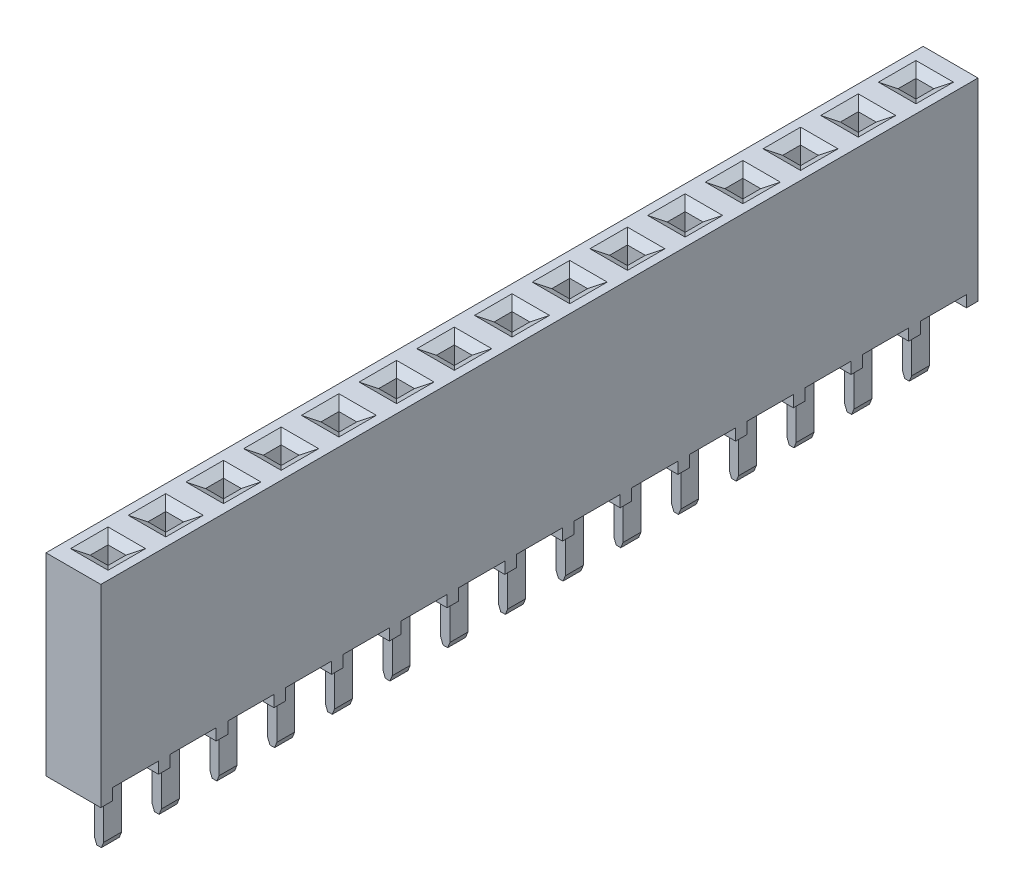
SolidWorks part; units mm, degrees
material "普通碳钢"
ref_plane "Front" through (0, 0, 0) normal (0, 0, 1) x (1, 0, 0)
ref_plane "Top" through (0, 0, 0) normal (0, 1, 0) x (1, 0, 0)
ref_plane "Right" through (0, 0, 0) normal (1, 0, 0) x (0, 0, -1)
sketch "Sketch1" plane through (0, 0, 0) normal (0, 1, 0) x (1, 0, 0)
  line L0 (-1.2065, -19.304) -> (1.2065, 19.304) construction
  line L1 (-1.2065, 19.304) -> (1.2065, 19.304)
  line L2 (-1.2065, 19.304) -> (-1.2065, -19.304)
  line L3 (-1.2065, -19.304) -> (1.2065, -19.304)
  line L4 (1.2065, 19.304) -> (1.2065, -19.304)
  dimension "D1" = 38.608
  dimension "D2" = 2.413
extrude "Main Body" add sketch "Sketch1" along normal blind 8.509
ref_plane "Plane1" through (0, 0, -15.24) normal (0, 0, -1) x (-1, 0, 0)
ref_plane "Plane2" through (0, 0, -17.78) normal (0, 0, -1) x (-1, 0, 0)
ref_plane "Plane3" through (0, 0, 0) normal (0, 0, 1) x (1, 0, 0)
ref_plane "Plane4" through (0, 0, -2.54) normal (0, 0, 1) x (1, 0, 0)
sketch "Sketch5" plane through (1.2065, 0, 0) normal (1, 0, 0) x (0, 0, -1)
  line L0 (-19.304, 0) -> (19.304, 0) construction
  line L1 (16.764, 0) -> (18.796, 0)
  line L2 (16.764, 0) -> (16.764, 0.508)
  line L3 (16.764, 0.508) -> (18.796, 0.508)
  line L4 (18.796, 0) -> (18.796, 0.508)
  line L5 (17.78, 0.7418) -> (17.78, -0.7099) construction
  line L6 (19.304, 8.509) -> (19.304, 0) construction
  dimension "D1" = 0.508
  dimension "D2" = 1.524
  dimension "D3" = 0.508
extrude "Cut-Extrude2" cut sketch "Sketch5" against normal up to next (2.413 mm away)
pattern_linear "LPattern1" count 15 spacing 2.54 along (0, 0, 1) of "Cut-Extrude2"
sketch "Sketch2" plane through (0, 8.509, 0) normal (0, 1, 0) x (-1, 0, 0)
  line L0 (0, -0.6833) -> (0, -4.4888) construction
  line L1 (-0.3937, -18.1737) -> (0.3937, -18.1737)
  line L2 (-0.3937, -18.1737) -> (-0.3937, -17.3863)
  line L3 (-0.3937, -17.3863) -> (0.3937, -17.3863)
  line L4 (0.3937, -18.1737) -> (0.3937, -17.3863)
  line L5 (0, 0) -> (-2.54, 0) construction
  line L6 (0.3937, -18.1737) -> (-0.3937, -17.3863) construction
  line L8 (-1.2065, -19.304) -> (1.2065, -19.304) construction
  line L9 (-1.2065, 19.304) -> (-1.2065, -19.304) construction
  point P8 (0, -17.78)
  dimension "D1" = 1.524
  dimension "D2" = 0.7874
  dimension "D3" = 0.7874
  dimension "D4" = 1.2065
extrude "Cut-Extrude1" cut sketch "Sketch2" against normal through all
chamfer "Chamfer1" distance 0.4318 angle 30 4 edges at (0.3937, 8.509, -17.78) (0, 8.509, -18.1737) (-0.3937, 8.509, -17.78) (0, 8.509, -17.3863)
pattern_linear "LPattern2" count 15 spacing 2.54 along (0, 0, 1) of "Chamfer1", "Cut-Extrude1"
sketch "Sketch4" plane through (0, 0, -17.78) normal (0, 0, -1) x (-1, 0, 0)
  line L0 (0, 2.0688) -> (0, -17.6627) construction
  line L1 (0.3937, 0.508) -> (0.3937, 8.2597) construction
  line L2 (-0.3937, 0.508) -> (-0.3937, 8.2597) construction
  line L3 (-0.3937, 1.016) -> (0.3937, 1.016)
  line L5 (-0.2032, 0.889) -> (-0.2032, -2.3876)
  line L6 (-0.1016, -2.6416) -> (0.1016, -2.6416)
  line L7 (0.2032, 0.889) -> (0.2032, -2.3876)
  line L8 (0.1016, -2.6416) -> (0.2032, -2.3876)
  line L9 (-0.2032, -2.3876) -> (-0.1016, -2.6416)
  line L10 (-1.2065, 0) -> (1.2065, 0) construction
  line L11 (0.3937, 1.016) -> (0.3937, 0.889)
  line L12 (0.3937, 0.889) -> (0.2032, 0.889)
  line L13 (-0.2032, 0.889) -> (-0.3937, 0.889)
  line L14 (-0.3937, 0.889) -> (-0.3937, 1.016)
  dimension "D1" = 0.254
  dimension "D2" = 0.2032
  dimension "D3" = 0.4064
  dimension "D4" = 2.6416
  dimension "D5" = 0.7874
  dimension "D6" = 0.889
  dimension "D7" = 1.016
extrude "PIN" add sketch "Sketch4" along normal mid plane 0.7874
pattern_linear "LPattern4" count 15 spacing 2.54 along (0, 0, 1) of "PIN"
sketch "Sketch7" plane through (0, 0, -17.78) normal (0, 0, -1) x (-1, 0, 0)
  line L0 (-0.2032, 1.016) -> (-0.2032, -0.9144)
  line L1 (0.6096, -1.3208) -> (1.4605, -1.3208)
  line L2 (1.4605, -1.3208) -> (1.4605, -1.7272)
  line L3 (1.4605, -1.7272) -> (0.6096, -1.7272)
  line L4 (0.2032, -0.9144) -> (0.2032, 1.016)
  line L5 (-0.2032, 1.016) -> (-0.3937, 1.016)
  line L6 (0, 1.4788) -> (0, -2.2478) construction
  line L10 (1.2065, 8.509) -> (1.2065, 0) construction
  line L11 (-0.3937, 1.016) -> (-0.3937, 1.27)
  line L12 (-0.3937, 1.27) -> (0.3937, 1.27)
  line L13 (0.3937, 1.27) -> (0.3937, 1.016)
  line L14 (0.3937, 1.016) -> (0.2032, 1.016)
  line L16 (1.4605, -1.524) -> (-2.3476, -1.524) construction
  line L17 (-1.2065, 0) -> (1.2065, 0) construction
  line L18 (1.2065, 0.508) -> (-1.2065, 0.508) construction
  arc A0 (-0.2032, -0.9144) -> (0.6096, -1.7272) centre (0.6096, -0.9144) ccw
  arc A1 (0.6096, -1.3208) -> (0.2032, -0.9144) centre (0.6096, -0.9144) cw
  dimension "D9" = 0.8128
  dimension "D10" = 0.4064
  dimension "D1" = 1.2065
  dimension "D2" = 0.4064
  dimension "D3" = 0.4064
  dimension "D4" = 1.524
  dimension "D6" = 0.7874
  dimension "D7" = 0.762
  dimension "D8" = 0.254
  dimension "A" = 0.254
sketch "Sketch8" plane through (0, 0, -15.24) normal (0, 0, -1) x (-1, 0, 0)
  line L0 (0.2032, 1.016) -> (0.2032, -0.9144)
  line L1 (-0.3937, 1.27) -> (0.3937, 1.27)
  line L2 (1.2065, 8.509) -> (1.2065, 0) construction
  line L3 (0.3937, 1.016) -> (0.2032, 1.016)
  line L5 (-0.3937, 1.016) -> (-0.3937, 1.27)
  line L6 (0.3937, 1.016) -> (0.3937, 1.27)
  line L7 (-1.2065, 0) -> (1.2065, 0) construction
  line L8 (-0.2032, 1.016) -> (-0.2032, -0.9144)
  line L9 (0, 1.9479) -> (0, -2.4889) construction
  line L10 (2.9301, -1.524) -> (0.4606, -1.524) construction
  line L11 (1.2065, 8.509) -> (1.2065, 0) construction
  line L13 (-0.2032, 1.016) -> (-0.2032, -3.4544)
  line L15 (0.6096, -1.7272) -> (1.4605, -1.7272)
  line L16 (1.4605, -1.7272) -> (1.4605, -1.3208)
  line L17 (1.4605, -1.3208) -> (0.6096, -1.3208)
  line L18 (0.6096, -4.2672) -> (1.4605, -4.2672)
  line L19 (0.2032, -3.4544) -> (0.2032, 1.016)
  line L20 (1.4605, -3.8608) -> (0.6096, -3.8608)
  line L21 (1.4605, -4.2672) -> (1.4605, -3.8608)
  line L22 (0.3937, 1.27) -> (-0.3937, 1.27)
  line L23 (-0.3937, 1.016) -> (-0.2032, 1.016)
  line L24 (0.2032, 1.016) -> (0.3937, 1.016)
  line L25 (0.3937, 1.016) -> (0.3937, 1.27)
  line L26 (-0.3937, 1.016) -> (-0.3937, 1.27)
  line L27 (0.3937, 0.508) -> (0.3937, 0.889) construction
  line L28 (-0.3937, 0.508) -> (-0.3937, 0.889) construction
  line L29 (0, 1.27) -> (0, -2.4889) construction
  line L30 (1.4605, -4.064) -> (1.27, -4.064) construction
  line L31 (-0.2032, 1.016) -> (-0.3937, 1.016)
  arc A0 (0.6096, -3.8608) -> (0.2032, -3.4544) centre (0.6096, -3.4544) cw
  arc A1 (0.6096, -4.2672) -> (-0.2032, -3.4544) centre (0.6096, -3.4544) cw
  arc A2 (0.6096, -1.7272) -> (-0.2032, -0.9144) centre (0.6096, -0.9144) cw
  arc A3 (0.6096, -1.3208) -> (0.2032, -0.9144) centre (0.6096, -0.9144) cw
  dimension "D5" = 0.8128
  dimension "D6" = 0.4064
  dimension "D14" = 0.4064
  dimension "D15" = 0.8128
  dimension "D1" = 1.27
  dimension "D2" = 0.254
  dimension "D3" = 0.4064
  dimension "D4" = 0.4064
  dimension "D7" = 1.524
  dimension "D8" = 0.4064
  dimension "D9" = 0.254
  dimension "D10" = 2.54
  dimension "D11" = 0.4064
  dimension "D12" = 1.2065
sketch "Sketch9" plane through (0, 0, -15.24) normal (0, 0, -1) x (-1, 0, 0)
  line L0 (0, 1.6049) -> (0, -3.2713) construction
  line L1 (-2.9337, 1.016) -> (-2.9337, 1.27)
  line L2 (0.3937, 1.27) -> (-0.3937, 1.27)
  line L4 (-2.1463, 1.27) -> (-2.9337, 1.27)
  line L5 (0.3937, 1.016) -> (0.3937, 1.27)
  line L6 (-2.3368, 1.016) -> (-2.1463, 1.016)
  line L7 (-0.3937, 1.016) -> (-0.3937, 1.27)
  line L8 (-0.3937, 1.016) -> (-0.2032, 1.016)
  line L10 (0.3937, 1.27) -> (-0.3937, 1.27)
  line L11 (-2.1463, 1.27) -> (-2.1463, 1.016)
  line L12 (-1.9304, -4.2672) -> (1.4605, -4.2672)
  line L13 (1.4605, -4.2672) -> (1.4605, -3.8608)
  line L14 (1.4605, -3.8608) -> (-1.9304, -3.8608)
  line L15 (0.2032, -5.9944) -> (0.2032, 1.016)
  line L16 (-0.3937, 1.016) -> (-0.3937, 1.27)
  line L17 (-0.2032, 1.016) -> (-0.2032, -5.9944)
  line L18 (-0.3937, 1.016) -> (-0.2032, 1.016)
  line L19 (0.2032, 1.016) -> (0.3937, 1.016)
  line L20 (0.3937, 1.27) -> (0.3937, 1.016)
  line L21 (0.2032, -0.9144) -> (0.2032, 1.016)
  line L22 (-0.2032, 1.016) -> (-0.2032, -0.9144)
  line L24 (1.2065, 8.509) -> (1.2065, 0) construction
  line L25 (1.4605, -1.7272) -> (1.4605, -1.3208)
  line L26 (1.4605, -1.3208) -> (0.6096, -1.3208)
  line L27 (-2.3368, -3.4544) -> (-2.3368, 1.016)
  line L29 (-2.7432, 1.016) -> (-2.7432, -3.4544)
  line L31 (-1.2065, 0) -> (1.2065, 0) construction
  line L32 (0.6096, -1.7272) -> (1.4605, -1.7272)
  line L34 (6.2865, -1.524) -> (4.283, -1.524) construction
  line L35 (6.2865, -4.064) -> (4.7316, -4.064) construction
  line L40 (-2.7432, 1.016) -> (-2.9337, 1.016)
  line L41 (-2.54, 1.27) -> (-2.54, -1.7272) construction
  line L42 (0.2032, 1.016) -> (0.3937, 1.016)
  line L43 (0.3937, 0.508) -> (0.3937, 0.889) construction
  line L44 (-0.3937, 0.508) -> (-0.3937, 0.889) construction
  line L45 (0, 1.27) -> (0, -1.198) construction
  line L46 (0.6096, -6.4008) -> (1.4605, -6.4008)
  line L47 (1.4605, -6.4008) -> (1.4605, -6.8072)
  line L48 (1.4605, -6.8072) -> (0.6096, -6.8072)
  line L49 (6.1112, -6.604) -> (4.5563, -6.604) construction
  arc A0 (0.2032, -0.9144) -> (0.6096, -1.3208) centre (0.6096, -0.9144) ccw
  arc A1 (-0.2032, -0.9144) -> (0.6096, -1.7272) centre (0.6096, -0.9144) ccw
  arc A2 (-1.9304, -4.2672) -> (-2.7432, -3.4544) centre (-1.9304, -3.4544) cw
  arc A3 (-1.9304, -3.8608) -> (-2.3368, -3.4544) centre (-1.9304, -3.4544) cw
  arc A4 (0.6096, -6.4008) -> (0.2032, -5.9944) centre (0.6096, -5.9944) cw
  arc A5 (0.6096, -6.8072) -> (-0.2032, -5.9944) centre (0.6096, -5.9944) cw
  dimension "D7" = 1.27
  dimension "D8" = 0.254
  dimension "D11" = 0.4064
  dimension "D12" = 0.8128
  dimension "D4" = 0.4064
  dimension "D5" = 0.8128
  dimension "D15" = 0.4064
  dimension "D16" = 0.8128
  dimension "D2" = 1.524
  dimension "D3" = 0.4064
  dimension "D6" = 0.4064
  dimension "D9" = 1.2065
  dimension "D10" = 2.54
  dimension "D13" = 0.4064
  dimension "D14" = 5.08
  dimension "D17" = 0.4064
  dimension "D18" = 2.54
  dimension "D19" = 0.7874
  dimension "D20" = 0.7874
  dimension "A" = 0.254
sketch "Sketch10" plane through (0, 0, -15.24) normal (0, 0, -1) x (-1, 0, 0)
  line L0 (-2.54, -14.478) -> (-2.54, 0.635)
  line L2 (-0.508, -16.51) -> (-0.2286, -16.51)
  line L3 (-1.2065, 0) -> (1.2065, 0) construction
  line L4 (1.2065, 8.509) -> (1.2065, 0) construction
  arc A0 (-2.54, -14.478) -> (-0.508, -16.51) centre (-0.508, -14.478) ccw
  dimension "D1" = 2.032
  dimension "D5" = 0.635
  dimension "D2" = 16.51
  dimension "D3" = 0.2794
  dimension "D4" = 3.7465
sketch "Sketch6" plane through (0, 0.508, 0) normal (0, 1, 0) x (-1, 0, 0)
  line L0 (-1.2065, -19.304) -> (1.2065, -19.304) construction
  line L3 (-1.7145, -18.6055) -> (-3.3655, -18.6055)
  line L6 (-3.3655, -18.6055) -> (-3.3655, -16.9545)
  line L8 (-3.3655, -16.9545) -> (-1.7145, -16.9545)
  line L10 (-1.7145, -16.9545) -> (-1.7145, -18.6055)
  line L11 (-3.3655, -17.78) -> (-1.7145, -17.78) construction
  line L12 (-2.54, -18.6055) -> (-2.54, -16.9545) construction
  line L14 (1.2065, -19.304) -> (1.2065, 19.304) construction
  dimension "D1" = 1.651
  dimension "D2" = 3.7465
  dimension "D3" = 1.524
sketch "Sketch11" plane through (0, 0, -15.24) normal (0, 0, -1) x (-1, 0, 0)
  line L0 (-0.2032, 1.016) -> (-0.2032, -0.4572)
  line L1 (-2.5781, -1.27) -> (-0.6096, -1.27)
  line L2 (-0.6096, -0.8636) -> (-2.5781, -0.8636)
  line L3 (-2.5781, -0.8636) -> (-2.5781, -1.27)
  line L4 (0.2032, -0.4572) -> (0.2032, 1.016)
  line L5 (0.3937, 1.27) -> (0.3937, 1.016)
  line L6 (0.3937, 1.016) -> (0.2032, 1.016)
  line L7 (0.3937, 1.27) -> (-0.3937, 1.27)
  line L8 (-0.3937, 1.27) -> (-0.3937, 1.016)
  line L9 (-0.3937, 1.016) -> (-0.2032, 1.016)
  line L10 (-0.3937, 0.508) -> (-0.3937, 0.889) construction
  line L11 (-1.2065, 8.509) -> (-1.2065, 0) construction
  line L12 (0, 1.27) -> (0, -1.1346) construction
  line L13 (-1.2065, 0) -> (1.2065, 0) construction
  arc A0 (-0.2032, -0.4572) -> (-0.6096, -0.8636) centre (-0.6096, -0.4572) cw
  arc A1 (-0.6096, -1.27) -> (0.2032, -0.4572) centre (-0.6096, -0.4572) ccw
  dimension "D7" = 1.27
  dimension "D4" = 0.4064
  dimension "D5" = 0.8128
  dimension "D1" = 0.4064
  dimension "D2" = 1.2065
  dimension "D3" = 1.27
  dimension "D6" = 0.4064
sketch "Sketch12" plane through (0, 0, -17.78) normal (0, 0, -1) x (-1, 0, 0)
  line L1 (0.3937, 1.27) -> (-0.3937, 1.27)
  line L3 (-0.3937, 1.016) -> (-0.2032, 1.016)
  line L5 (0.3937, 1.016) -> (0.3937, 1.27)
  line L6 (0, 1.27) -> (0, -2.7927) construction
  line L7 (2.5781, -0.8636) -> (2.5781, -1.27)
  line L8 (2.5781, -1.27) -> (0.6096, -1.27)
  line L9 (0.6096, -0.8636) -> (2.5781, -0.8636)
  line L10 (0.2032, 1.016) -> (0.3937, 1.016)
  line L11 (1.2065, 8.509) -> (1.2065, 0) construction
  line L12 (0.2032, -0.4572) -> (0.2032, 1.016)
  line L13 (-1.2065, 0) -> (1.2065, 0) construction
  line L14 (-0.2032, 1.016) -> (-0.2032, -0.4572)
  line L19 (-0.3937, 1.016) -> (-0.3937, 1.27)
  arc A0 (0.6096, -0.8636) -> (0.2032, -0.4572) centre (0.6096, -0.4572) cw
  arc A1 (0.6096, -1.27) -> (-0.2032, -0.4572) centre (0.6096, -0.4572) cw
  dimension "D7" = 1.27
  dimension "D11" = 0.8128
  dimension "D3" = 1.2065
  dimension "D4" = 0.7874
  dimension "D5" = 1.27
  dimension "D6" = 0.254
  dimension "D8" = 0.4064
  dimension "D10" = 0.4064
sketch "Sketch19" plane through (0, 0, 0) normal (0, 0, 1) x (1, 0, 0)
  line L0 (-3.1115, -1.7272) -> (-2.8964, -1.7272)
  line L1 (-1.5486, -1.7272) -> (-1.3335, -1.7272)
  line L2 (-1.3335, -1.7272) -> (-1.3335, -1.3208)
  line L3 (-1.3335, -1.3208) -> (-3.1115, -1.3208)
  line L4 (-3.1115, -1.3208) -> (-3.1115, -1.7272)
  line L6 (-3.1115, -1.9304) -> (-0.9396, -1.9304) construction
  line L7 (-3.1115, -1.524) -> (-1.3335, -1.524) construction
  line L8 (8.4718, 0) -> (-8.4718, 0) construction
  line L9 (-1.2065, 8.509) -> (-1.2065, 0) construction
  line L10 (-2.2225, -1.1176) -> (-2.2225, -1.524) construction
  arc A0 (-2.6718, -1.7949) -> (-2.8964, -1.7272) centre (-2.8964, -2.1336) ccw
  arc A1 (-2.6718, -1.7949) -> (-1.7732, -1.7949) centre (-2.2225, -1.1176) ccw
  arc A2 (-1.5486, -1.7272) -> (-1.7732, -1.7949) centre (-1.5486, -2.1336) ccw
  dimension "D1" = 0.8128
  dimension "D6" = 0.4064
  dimension "D2" = 1.524
  dimension "D3" = 0.4064
  dimension "D4" = 0.2032
  dimension "D5" = 1.016
  dimension "D7" = 1.778
sketch "Sketch20" plane through (0, 0, 0) normal (0, 0, 1) x (1, 0, 0)
  line L0 (-2.5334, -1.524) -> (-1.2951, -1.524) construction
  line L1 (-1.2065, 8.509) -> (-1.2065, 0) construction
  line L4 (-2.8964, -1.3208) -> (-3.1115, -1.3208)
  line L5 (-3.1115, -1.3208) -> (-3.1115, -1.0668)
  line L6 (-3.1115, -1.0668) -> (-1.3335, -1.0668)
  line L7 (-1.5486, -1.3208) -> (-1.3335, -1.3208)
  line L8 (-1.3335, -1.3208) -> (-1.3335, -1.0668)
  line L9 (-2.2225, -1.524) -> (-2.2225, -0.6068) construction
  line L10 (-1.2065, 0) -> (1.2065, 0) construction
  arc A0 (-2.6718, -1.3885) -> (-1.7732, -1.3885) centre (-2.2225, -0.7112) ccw
  arc A1 (-2.6718, -1.3885) -> (-2.8964, -1.3208) centre (-2.8964, -1.7272) ccw
  arc A2 (-1.7732, -1.3885) -> (-1.5486, -1.3208) centre (-1.5486, -1.7272) cw
  dimension "D1" = 1.6256
  dimension "D4" = 0.4064
  dimension "D2" = 1.016
  dimension "D3" = 1.524
  dimension "D5" = 0.254
  dimension "D6" = 0.4064
  dimension "D7" = 1.778
sketch "Sketch45" plane through (0, 0, -2.54) normal (0, 0, 1) x (1, 0, 0)
  line L0 (-3.1115, -1.3208) -> (-3.048, -1.3208)
  line L1 (-1.3335, -1.3208) -> (-3.1115, -1.3208) construction
  line L2 (-2.931, -1.3036) -> (-2.398, -1.1434)
  line L3 (-2.047, -1.1434) -> (-1.514, -1.3036)
  line L4 (-1.397, -1.3208) -> (-1.3335, -1.3208)
  line L5 (-1.3335, -1.3208) -> (-1.3335, -1.7272)
  line L6 (-1.3335, -1.7272) -> (-3.1115, -1.7272)
  line L7 (-3.1115, -1.7272) -> (-3.1115, -1.3208)
  arc A0 (-3.048, -1.3208) -> (-2.931, -1.3036) centre (-3.048, -0.9144) ccw
  arc A1 (-2.398, -1.1434) -> (-2.047, -1.1434) centre (-2.2225, -1.7272) cw
  arc A2 (-1.514, -1.3036) -> (-1.397, -1.3208) centre (-1.397, -0.9144) ccw
  dimension "D1" = 0.2032
  dimension "D2" = 0.0635
  dimension "D3" = 0.4064
  dimension "D4" = 0.6096
sketch "Sketch46" plane through (0, 0, -2.54) normal (0, 0, 1) x (1, 0, 0)
  line L1 (-1.5486, -1.3208) -> (-1.3335, -1.3208) construction
  line L3 (-3.1115, -1.3208) -> (-3.1115, -1.0668) construction
  line L4 (-3.1115, -1.0668) -> (-1.3335, -1.0668) construction
  line L5 (-1.3335, -1.3208) -> (-1.3335, -1.0668) construction
  line L6 (-2.8964, -1.3208) -> (-3.1115, -1.3208) construction
  line L10 (-1.2951, -1.524) -> (-3.1115, -1.524) construction
  line L11 (-3.1115, -1.9812) -> (-1.3335, -1.9812)
  line L12 (-3.1115, -1.7272) -> (-3.1115, -1.9812)
  line L13 (-2.8964, -1.7272) -> (-3.1115, -1.7272)
  line L14 (-1.5486, -1.7272) -> (-1.3335, -1.7272)
  line L15 (-1.3335, -1.7272) -> (-1.3335, -1.9812)
  arc A0 (-2.6718, -1.3885) -> (-1.7732, -1.3885) centre (-2.2225, -0.7112) ccw construction
  arc A3 (-2.6718, -1.3885) -> (-2.8964, -1.3208) centre (-2.8964, -1.7272) ccw construction
  arc A6 (-2.6718, -1.6595) -> (-2.8964, -1.7272) centre (-2.8964, -1.3208) cw
  arc A7 (-1.5486, -1.7272) -> (-1.7732, -1.6595) centre (-1.5486, -1.3208) cw
  arc A8 (-2.6718, -1.6595) -> (-1.7732, -1.6595) centre (-2.2225, -2.3368) cw
sketch "Sketch27" plane through (0, 0, 0) normal (0, 0, 1) x (1, 0, 0)
  line L0 (-3.8171, -6.1976) -> (-2.3191, -6.1976) construction
  line L3 (-2.2225, -7.0104) -> (-2.2225, -2.6186) construction
  line L4 (-1.2065, 8.509) -> (-1.2065, 0) construction
  line L5 (-2.8964, -6.4008) -> (-3.1115, -6.4008)
  line L6 (-3.1115, -6.4008) -> (-3.1115, -6.8072)
  line L7 (-3.1115, -6.8072) -> (-1.3335, -6.8072)
  line L8 (-1.3335, -6.8072) -> (-1.3335, -6.4008)
  line L9 (-1.3335, -6.4008) -> (-1.5486, -6.4008)
  line L10 (-3.1115, -6.604) -> (-1.3335, -6.604) construction
  line L11 (-1.2065, 0) -> (1.2065, 0) construction
  arc A0 (-1.7732, -6.3331) -> (-2.6718, -6.3331) centre (-2.2225, -7.0104) ccw
  arc A1 (-1.5486, -6.4008) -> (-1.7732, -6.3331) centre (-1.5486, -5.9944) cw
  arc A2 (-2.8964, -6.4008) -> (-2.6718, -6.3331) centre (-2.8964, -5.9944) ccw
  dimension "D1" = 1.6256
  dimension "D7" = 0.4064
  dimension "D2" = 0.4064
  dimension "D3" = 1.016
  dimension "D5" = 0.4064
  dimension "D6" = 1.778
sketch "Sketch28" plane through (0, 0, 0) normal (0, 0, 1) x (1, 0, 0)
  line L0 (-4.004, -6.604) -> (-2.6238, -6.604) construction
  line L3 (-2.2225, -7.4168) -> (-2.2225, -2.6456) construction
  line L4 (-1.2065, 8.509) -> (-1.2065, 0) construction
  line L5 (-1.2065, 0) -> (1.2065, 0) construction
  line L6 (-2.8964, -6.8072) -> (-3.1115, -6.8072)
  line L7 (-3.1115, -6.8072) -> (-3.1115, -7.0612)
  line L8 (-3.1115, -7.0612) -> (-1.3335, -7.0612)
  line L9 (-1.3335, -7.0612) -> (-1.3335, -6.8072)
  line L10 (-1.3335, -6.8072) -> (-1.5486, -6.8072)
  arc A0 (-1.7732, -6.7395) -> (-2.6718, -6.7395) centre (-2.2225, -7.4168) ccw
  arc A1 (-1.5486, -6.8072) -> (-1.7732, -6.7395) centre (-1.5486, -6.4008) cw
  arc A2 (-2.8964, -6.8072) -> (-2.6718, -6.7395) centre (-2.8964, -6.4008) ccw
  dimension "D1" = 1.6256
  dimension "D7" = 0.4064
  dimension "D3" = 1.016
  dimension "D4" = 0.2032
  dimension "D5" = 0.254
  dimension "D6" = 1.778
sketch "Sketch38" plane through (0, 0, -2.54) normal (0, 0, 1) x (1, 0, 0)
  line L0 (-1.016, -1.016) -> (2.1645, -1.016) construction
  line L1 (0, -1.905) -> (0, -0.127) construction
  line L2 (0.4064, -0.4657) -> (0.4064, -2.0349) construction
  line L5 (0.2032, -0.1782) -> (0.2032, -0.127)
  line L6 (0.2032, -0.127) -> (-0.2032, -0.127)
  line L7 (-0.2032, -0.127) -> (-0.2032, -1.905)
  line L8 (-1.2065, 0) -> (1.2065, 0) construction
  line L9 (-0.2032, -1.905) -> (0.2032, -1.905)
  line L10 (0.2032, -1.905) -> (0.2032, -1.8538)
  line L12 (-1.2065, 8.509) -> (-1.2065, 0) construction
  arc A0 (0.2032, -0.1782) -> (0.2484, -0.3644) centre (0.6096, -0.1782) ccw
  arc A1 (0.2484, -1.6676) -> (0.2484, -0.3644) centre (-1.016, -1.016) ccw
  arc A2 (0.2032, -1.8538) -> (0.2484, -1.6676) centre (0.6096, -1.8538) cw
  dimension "D1" = 1.4224
  dimension "D5" = 0.4064
  dimension "D4" = 1.778
  dimension "D6" = 0.4064
  dimension "D2" = 1.2065
  dimension "D3" = 1.016
  dimension "D7" = 0.4064
sketch "Sketch39" plane through (0, 0, -2.54) normal (0, 0, 1) x (1, 0, 0)
  line L0 (-1.4224, -1.016) -> (1.423, -1.016) construction
  line L1 (0, -1.016) -> (0, -2.3641) construction
  line L2 (-1.2065, 8.509) -> (-1.2065, 0) construction
  line L3 (-1.2065, 0) -> (1.2065, 0) construction
  line L4 (-0.2032, -0.2834) -> (-0.2032, -0.127)
  line L5 (-0.2032, -0.127) -> (-0.4572, -0.127)
  line L6 (-0.4572, -0.127) -> (-0.4572, -1.905)
  line L7 (-0.4572, -1.905) -> (-0.2032, -1.905)
  line L8 (-0.2032, -1.905) -> (-0.2032, -1.7486)
  arc A0 (-0.2032, -1.7486) -> (-0.2032, -0.2834) centre (-1.4224, -1.016) ccw
  dimension "D1" = 2.8448
  dimension "D2" = 1.016
  dimension "D3" = 0.1564
  dimension "D4" = 0.254
  dimension "D5" = 1.778
  dimension "D6" = 1.2065
sketch "Sketch40" plane through (0, 8.509, 0) normal (0, 1, 0) x (-1, 0, 0)
  circle A0 centre (0, 0) radius 1.7526
  dimension "D1" = 3.5052
sketch "Sketch41" plane through (0, 0, 0) normal (0, 0, 1) x (1, 0, 0)
  line L0 (0, 0) -> (0, 12.0579) construction
  line L1 (-2.8283, 4.7606) -> (-2.8141, 4.7868)
  line L2 (-2.6496, 5.6392) -> (-2.9701, 8.4292)
  line L3 (-2.7178, 8.7122) -> (2.7178, 8.7122)
  line L4 (-2.9718, 10.4747) -> (-2.9718, 5.0805) construction
  line L7 (-2.7178, 8.509) -> (2.7178, 8.509)
  line L8 (-2.4477, 5.6624) -> (-2.7683, 8.4524)
  line L9 (2.8283, 4.7606) -> (2.6354, 4.6902)
  line L10 (-2.8283, 4.7606) -> (-2.6354, 4.6902)
  line L11 (2.4477, 5.6624) -> (2.7683, 8.4524)
  line L12 (2.6496, 5.6392) -> (2.9701, 8.4292)
  line L13 (2.8283, 4.7606) -> (2.8141, 4.7868)
  line L14 (-1.2065, 0) -> (1.2065, 0) construction
  arc A0 (-2.9701, 8.4292) -> (-2.7178, 8.7122) centre (-2.7178, 8.4582) cw
  arc A1 (-2.8141, 4.7868) -> (-2.6496, 5.6392) centre (-4.0849, 5.4742) ccw
  arc A2 (-2.7683, 8.4524) -> (-2.7178, 8.509) centre (-2.7178, 8.4582) cw
  arc A3 (-2.6354, 4.6902) -> (-2.4477, 5.6624) centre (-4.0849, 5.4742) ccw
  arc A4 (2.6354, 4.6902) -> (2.4477, 5.6624) centre (4.0849, 5.4742) cw
  arc A5 (2.7683, 8.4524) -> (2.7178, 8.509) centre (2.7178, 8.4582) ccw
  arc A6 (2.8141, 4.7868) -> (2.6496, 5.6392) centre (4.0849, 5.4742) cw
  arc A7 (2.9701, 8.4292) -> (2.7178, 8.7122) centre (2.7178, 8.4582) ccw
  point P6 (0, 8.7122)
  point P31 (0, 8.509)
  dimension "D1" = 0.254
  dimension "D4" = 0.2032
  dimension "D6" = 1.4448
  dimension "D2" = 8.7122
  dimension "D3" = 2.9718
  dimension "D5" = 3.9516
  dimension "D7" = 2.79
  dimension "D8" = 0.3206
  dimension "D9" = 4.022
sketch "Sketch43" plane through (0, 8.509, 0) normal (0, 1, 0) x (-1, 0, 0)
  line L0 (2.4765, 0) -> (-2.4765, 0) construction
  line L1 (2.4765, -5.0165) -> (-2.4765, -5.0165)
  line L2 (2.4765, -5.0165) -> (2.4765, 5.0165)
  line L3 (2.4765, 5.0165) -> (-2.4765, 5.0165)
  line L4 (-2.4765, -5.0165) -> (-2.4765, 5.0165)
  dimension "D1" = 10.033
  dimension "D2" = 4.953
sketch "Polarize sketch" plane through (0, 8.509, 0) normal (0, 1, 0) x (-1, 0, 0)
  line L0 (-0.8915, -20.1905) -> (0.8865, -18.4125) construction
  line L1 (-0.8915, -20.1905) -> (0.8865, -20.1905)
  line L2 (-0.8915, -20.1905) -> (-0.8915, -18.4125)
  line L3 (-0.8915, -18.4125) -> (0.8865, -18.4125)
  line L4 (0.8865, -20.1905) -> (0.8865, -18.4125)
  line L5 (0.8865, -20.1905) -> (-0.0025, -19.3015) construction
  line L6 (0, -7.5404) -> (0, -10.8194) construction
  line L7 (-1.2065, -19.304) -> (1.2065, -19.304) construction
  line L11 (1.2065, -19.304) -> (1.2065, 19.304) construction
  dimension "D1" = 1.2065
  dimension "D2" = 1.778
  dimension "Width" = 0.0025
  dimension "Height" = 0.0025
sketch "Sketch44" plane through (0, 0, -19.304) normal (0, 0, -1) x (-1, 0, 0)
  line L0 (-1.2065, 5.4864) -> (-0.8255, 4.9784)
  line L1 (-1.2065, 8.509) -> (-1.2065, 0) construction
  line L2 (-0.8255, 4.2164) -> (-1.2065, 3.7084)
  line L3 (-1.2065, 3.7084) -> (-1.2065, 5.4864)
  line L4 (-1.3335, 4.5974) -> (-1.2065, 4.5974) construction
  line L5 (-1.2065, 8.509) -> (1.2065, 8.509) construction
  arc A0 (-0.8255, 4.9784) -> (-0.8255, 4.2164) centre (-1.3335, 4.5974) cw
  dimension "D3" = 0.508
  dimension "D4" = 0.635
  dimension "D1" = 1.778
  dimension "D2" = 3.9116
